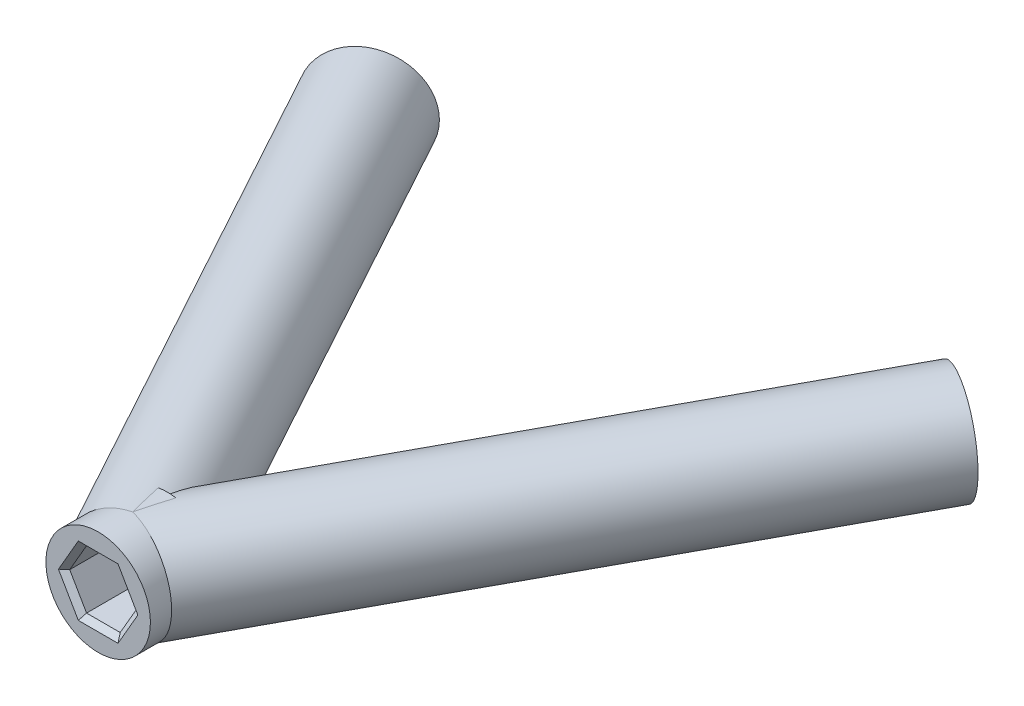
SolidWorks part; units mm, degrees
material "ABS"
ref_plane "Front Plane" through (0, 0, 0) normal (0, 0, 1) x (1, 0, 0)
ref_plane "Top Plane" through (0, 0, 0) normal (0, 1, 0) x (1, 0, 0)
ref_plane "Right Plane" through (0, 0, 0) normal (1, 0, 0) x (0, 0, -1)
sketch "Sketch1" plane through (0, 0, 0) normal (0, 1, 0) x (1, 0, 0)
  line L0 (0, 0) -> (36.1483, 87.2697) construction
  line L1 (0, 0) -> (-35.5896, 85.9208) construction
  line L2 (0, 0) -> (0, 97.1253) construction
  line L11 (0, 0) -> (0, -18.024) construction
  line L12 (0, 17.5) -> (0, 24.1)
  point P3 (-24.4917, 59.1283)
  point P6 (25.0505, 60.4772)
  point P8 (0, 17.5)
  point P9 (-27.0175, 65.2259)
  point P10 (27.5762, 66.5748)
  point P26 (0, 15.6788)
  point P27 (31.3933, 91.469)
  point P28 (36.9366, 89.1729)
  point P29 (42.4799, 86.8768)
  point P30 (0, -15.6788)
  dimension "D8" = 17.5
  dimension "D10" = 22.4
  dimension "D1" = 94.46
  dimension "D2" = 93
  dimension "D3" = 45
  dimension "D4" = 22.5
  dimension "D5" = 29
  dimension "D6" = 29
  dimension "D7" = 6.6
  dimension "D9" = 22.4
revolve "Revolve-Thin1" add sketch "Sketch1" angle 360 about L12 wall 5
sketch "Sketch18" plane through (0, 0, -17.5) normal (0, 0, 1) x (1, 0, 0)
  line L1 (1.6108, 2.79) -> (-1.6108, 2.79)
  line L2 (-1.6108, 2.79) -> (-3.2216, 0)
  line L3 (-3.2216, 0) -> (-1.6108, -2.79)
  line L4 (-1.6108, -2.79) -> (1.6108, -2.79)
  line L5 (1.6108, -2.79) -> (3.2216, 0)
  line L6 (3.2216, 0) -> (1.6108, 2.79)
  circle A0 centre (0, 0) radius 2.79 construction
  dimension "D1" = 5.58
sketch "Sketch19" plane through (0, 0, 0) normal (0, 1, 0) x (1, 0, 0)
  line L0 (0, 17.5) -> (0, 24.1) construction
  line L1 (0, 17.5) -> (0, 24.1) construction
  line L2 (-35.5896, 85.9208) -> (0, 20.8) construction
  line L3 (0, 20.8) -> (36.1483, 87.2697)
  line L4 (0, 20.8) -> (0, 96.8929) construction
  line L5 (-27.1971, 70.5645) -> (0, 20.8)
  point P2 (0, 20.8)
  point P6 (-27.1971, 70.5645)
  point P9 (27.7876, 71.896)
  dimension "D1" = 17.5
  dimension "D2" = 17.5
  dimension "D3" = 28.657
  dimension "D4" = 28.539
  dimension "D5" = 56.7114
  dimension "D6" = 58.1632
  dimension "D7" = 74.2114
  dimension "D8" = 75.6632
sketch "Sketch20" plane through (0, 0, 0) normal (0, 1, 0) x (1, 0, 0)
  line L0 (36.1483, 87.2697) -> (0, 20.8) construction
  line L1 (0, 17.5) -> (0, 24.1) construction
  line L2 (25.4466, 67.5914) -> (0, 20.8)
  point P5 (25.4466, 67.5914)
  dimension "D1" = 22.4
sketch3d "3DSketch1"
  line L0 (-27.1971, 0, -70.5645) -> (0, 0, -20.8) construction
sketch "Sketch21" plane through (-35.9502, 0, -65.7807) normal (0.4796, 0, 0.8775) x (0.8775, 0, -0.4796)
  circle A0 centre (9.9751, 0) radius 5
  dimension "D1" = 10
extrude "Boss-Extrude1" add sketch "Sketch21" along normal up to next
sketch3d "3DSketch2"
  line L1 (0, 0, -20.8) -> (36.1483, 0, -87.2697) construction
sketch "Sketch22" plane through (36.5174, 0, -67.1485) normal (-0.4778, 0, 0.8785) x (0.8785, 0, 0.4778)
  circle A0 centre (-9.9373, 0) radius 5
  dimension "D1" = 10
extrude "Boss-Extrude2" add sketch "Sketch22" along normal up to next
sketch3d "3DSketch3"
  line L0 (0, 0, 0) -> (0, 0, -97.1253) construction
  line L1 (0, 0, 0) -> (-35.5896, 0, -85.9208) construction
sketch "Sketch29" plane through (-35.9502, 0, -65.7807) normal (-0.4796, 0, -0.8775) x (-0.8775, 0, 0.4796)
  line L0 (-9.9751, 5) -> (-9.9751, -5) construction
  line L1 (-7.291, 1.7818) -> (-10.1761, 3.2153)
  line L2 (-10.1761, 3.2153) -> (-12.8602, 1.4335)
  line L3 (-12.8602, 1.4335) -> (-12.6591, -1.7818)
  line L4 (-12.6591, -1.7818) -> (-9.774, -3.2153)
  line L5 (-9.774, -3.2153) -> (-7.09, -1.4335)
  line L6 (-7.09, -1.4335) -> (-7.291, 1.7818)
  line L7 (-14.9751, 0) -> (-4.9751, 0) construction
  line L8 (-10.1761, 3.2153) -> (-9.774, -3.2153) construction
  circle A0 centre (-9.9751, 0) radius 2.79 construction
  circle A1 centre (-9.9751, 0) radius 5 construction
  arc A2 (-11.5546, 4.7439) -> (-11.5546, -4.7439) centre (-9.9751, 0) ccw construction
  dimension "D1" = 5.58
  dimension "D2" = 3.578
extrude "Cut-Extrude3" cut sketch "Sketch29" against normal blind 6.6
sketch "Sketch30" plane through (36.5174, 0, -67.1485) normal (0.4778, 0, -0.8785) x (-0.8785, 0, -0.4778)
  line L0 (9.9373, 5) -> (9.9373, -5) construction
  line L1 (12.8224, 1.4335) -> (10.1383, 3.2153)
  line L2 (10.1383, 3.2153) -> (7.2532, 1.7818)
  line L3 (7.2532, 1.7818) -> (7.0522, -1.4335)
  line L4 (7.0522, -1.4335) -> (9.7362, -3.2153)
  line L5 (9.7362, -3.2153) -> (12.6213, -1.7818)
  line L6 (12.6213, -1.7818) -> (12.8224, 1.4335)
  line L8 (10.1383, 3.2153) -> (9.7362, -3.2153) construction
  circle A0 centre (9.9373, 0) radius 2.79 construction
  circle A4 centre (9.9373, 0) radius 5 construction
  circle A5 centre (9.9373, 0) radius 5
  dimension "D1" = 5.58
  dimension "D2" = 3.578
extrude "Cut-Extrude4" cut sketch "Sketch30" against normal blind 6.6 contours L5 L6 L1 L2 L3 L4
extrude "Cut-Extrude5" cut sketch "Sketch18" against normal blind 6.6
chamfer "Chamfer2" distance 0.5 angle 45 18 edges at (0, 2.79, -17.5) (2.4162, 1.395, -17.5) (2.4162, -1.395, -17.5) (0, -2.79, -17.5) (-2.4162, -1.395, -17.5) (-2.4162, 1.395, -17.5) (-29.6405, 0.1741, -69.2291) (-28.5512, -2.3244, -69.8245) (-26.1077, -2.4986, -71.1599) (-24.7536, -0.1741, -71.8999) (-25.843, 2.3244, -71.3045) (-28.2865, 2.4986, -69.9691) (25.3414, -0.1741, -73.2263) (26.697, -2.4986, -72.4891) (29.1432, -2.3244, -71.1588) (30.2338, 0.1741, -70.5657) (28.8782, 2.4986, -71.3029) (26.432, 2.3244, -72.6332)
sketch3d "3DSketch4"
  line L0 (0, 0, -17.5) -> (0, 0, -24.1) construction
  line L1 (0, 0, -17.5) -> (0, 0, -24.1)
  line L2 (0, 0, -20.8) -> (27.7876, 0, -71.896)
  point P2 (0, 0, -20.8)
sketch3d "3DSketch5" plane through (0, 0, 0) normal (0, 0, 1) x (1, 0, 0)
